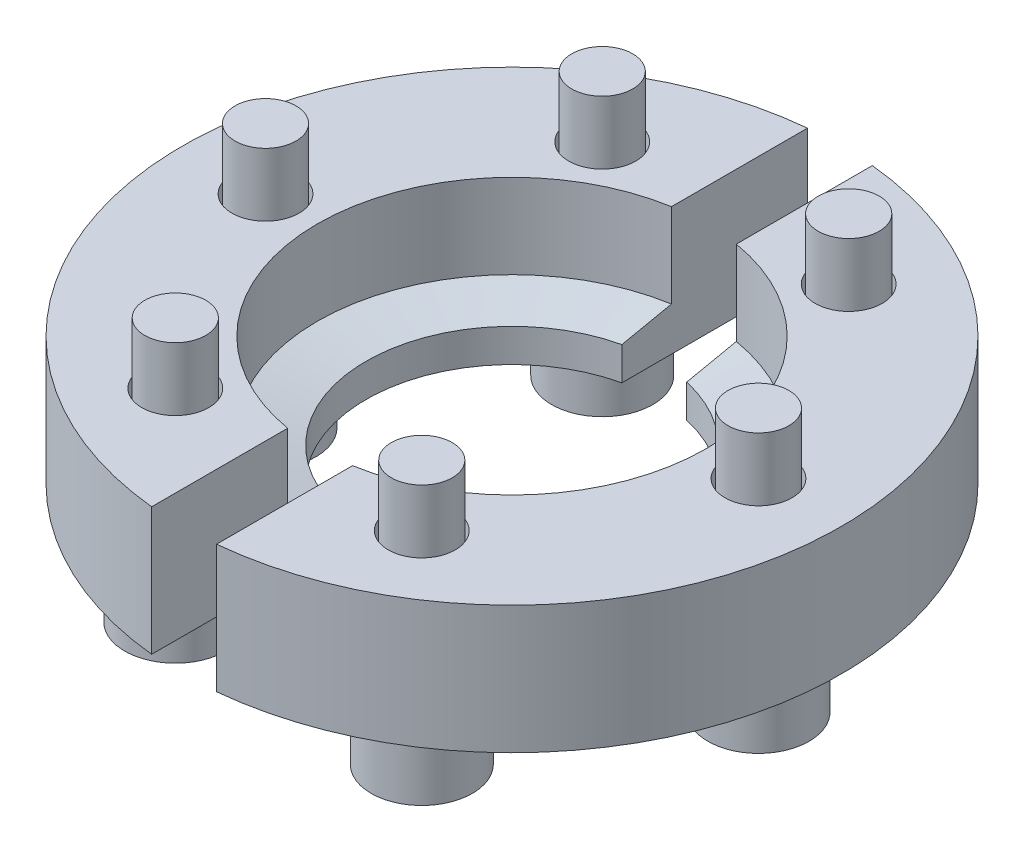
SolidWorks part; units mm, degrees
material "6061-T6 (SS)"
ref_plane "Front Plane" through (0, 0, 0) normal (0, 0, 1) x (1, 0, 0)
ref_plane "Top Plane" through (0, 0, 0) normal (0, 1, 0) x (1, 0, 0)
ref_plane "Right Plane" through (0, 0, 0) normal (1, 0, 0) x (0, 0, -1)
sketch "Sketch1" plane through (0, 0, 0) normal (0, 1, 0) x (1, 0, 0)
  circle A0 centre (0, 0) radius 25.4
  dimension "D1" = 50.8
extrude "Boss-Extrude1" add sketch "Sketch1" along normal blind 9.85
sketch "Sketch2" plane through (0, 0, 0) normal (0, 0, 1) x (1, 0, 0)
  line L0 (11.25, 0) -> (11.25, 2.5529)
  line L1 (-25.4, 0) -> (25.4, 0) construction
  line L2 (11.25, 2.5529) -> (15, 3.35)
  line L3 (15, 3.35) -> (15, 9.85)
  line L4 (25.4, 9.85) -> (-25.4, 9.85) construction
  line L5 (15, 9.85) -> (0, 9.85)
  line L6 (0, 9.85) -> (0, 0)
  line L7 (0, 0) -> (11.25, 0)
  line L8 (0, 0) -> (0, -3.744) construction
  dimension "D1" = 30
  dimension "D2" = 6.5
  dimension "D3" = 22.5
  dimension "D4" = 78
revolve "Cut-Revolve1" cut sketch "Sketch2" angle 360 about L8
sketch "Sketch3" plane through (0, 9.85, 0) normal (0, 1, 0) x (1, 0, 0)
  line L0 (0, 0) -> (0, -3.5728) construction
  circle A0 centre (19, 0) radius 2.585
  dimension "D1" = 38
  dimension "D2" = 5.17
extrude "Cut-Extrude1" cut sketch "Sketch3" against normal through all
pattern_circular "CirPattern1" count 6 over 360 about axis through (0, 0, 0) along (0, 1, 0) of "Cut-Extrude1"
sketch "Sketch4" plane through (0, 9.85, 0) normal (0, 1, 0) x (1, 0, 0)
  line L0 (-2.5, 25.2767) -> (-2.5, -25.2767)
  line L1 (2.5, -25.2767) -> (2.5, 25.2767)
  line L2 (0, 0) -> (0, 6.0027) construction
  line L3 (0, 6.0027) -> (2.5, 6.0027) construction
  line L4 (0, 6.0027) -> (-2.5, 6.0027) construction
  line L5 (0, 0) -> (11.0132, 0) construction
  circle A0 centre (0, 0) radius 25.4 construction
  arc A1 (-2.5, -25.2767) -> (2.5, -25.2767) centre (0, 0) ccw
  arc A2 (2.5, 25.2767) -> (-2.5, 25.2767) centre (0, 0) ccw
  dimension "D1" = 5
  dimension "D2" = 90
extrude "Cut-Extrude2" cut sketch "Sketch4" against normal through all
sketch "Sketch5" plane through (0, 0, 0) normal (0, -1, 0) x (1, 0, 0)
  circle A0 centre (19, 0) radius 2.7
  circle A1 centre (19, 0) radius 4.93
  dimension "D1" = 5.4
  dimension "D2" = 9.86
extrude "Boss-Extrude2" add sketch "Sketch5" along normal blind 0.95 separate body
sketch "Sketch7" plane through (0, 0, 0) normal (0, 0, 1) x (1, 0, 0)
  line L0 (19, -0.95) -> (19, 14.55) construction
  line L1 (14.07, -0.95) -> (23.93, -0.95) construction
  line L2 (19, 14.55) -> (21.35, 14.55)
  line L3 (21.35, 14.55) -> (21.35, -0.95)
  line L4 (21.35, -0.95) -> (22.9, -0.95)
  line L5 (22.9, -0.95) -> (22.9, -5.75)
  line L6 (22.9, -5.75) -> (19, -5.75)
  line L7 (19, -5.75) -> (19, 14.55)
  line L8 (19, 14.55) -> (19, 17.1971) construction
  dimension "D1" = 4.8
  dimension "D2" = 7.8
  dimension "D3" = 4.7
  dimension "D4" = 20.3
revolve "Revolve1" add sketch "Sketch7" angle 360 about L8
sketch "Sketch8" plane through (0, -5.75, 0) normal (0, -1, 0) x (1, 0, 0)
  line L1 (19, 2.3383) -> (16.975, 1.1691)
  line L2 (16.975, 1.1691) -> (16.975, -1.1691)
  line L3 (16.975, -1.1691) -> (19, -2.3383)
  line L4 (19, -2.3383) -> (21.025, -1.1691)
  line L5 (21.025, -1.1691) -> (21.025, 1.1691)
  line L6 (21.025, 1.1691) -> (19, 2.3383)
  circle A0 centre (19, 0) radius 2.025 construction
  dimension "D1" = 4.05
extrude "Cut-Extrude3" cut sketch "Sketch8" against normal blind 3.2
pattern_circular "CirPattern2" count 6 over 360 about axis through (0, 0, 0) along (0, 1, 0) of bodies 112 114
ref_plane "Plane1" through (0, 8.35, 0) normal (0, 1, 0) x (1, 0, 0)
